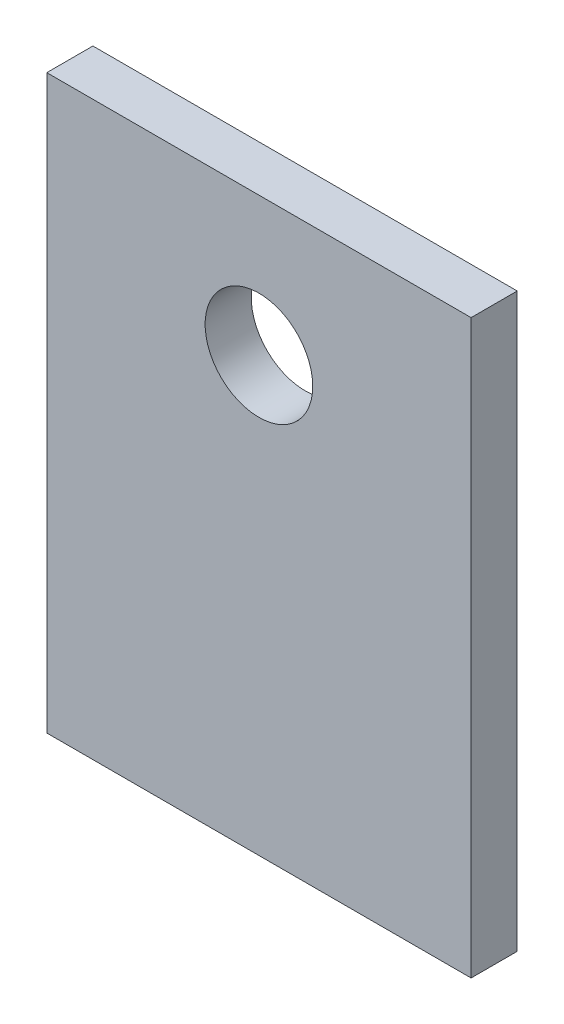
SolidWorks part; units mm, degrees
material "Медь"
ref_plane "Спереди" through (0, 0, 0) normal (0, 0, 1) x (1, 0, 0)
ref_plane "Сверху" through (0, 0, 0) normal (0, 1, 0) x (1, 0, 0)
ref_plane "Справа" through (0, 0, 0) normal (1, 0, 0) x (0, 0, -1)
sketch "Эскиз1" plane through (0, 0, 0) normal (0, 0, 1) x (-1, 0, 0)
  line L0 (-6.9, -9.3) -> (6.9, -9.3)
  line L2 (6.9, -9.3) -> (6.9, 9.3)
  line L4 (6.9, 9.3) -> (-6.9, 9.3)
  line L6 (-6.9, 9.3) -> (-6.9, -9.3)
  circle A1 centre (0, -4.79) radius 1.75
extrude "Бобышка-Вытянуть2" add sketch "Эскиз1" along normal blind 1.5
